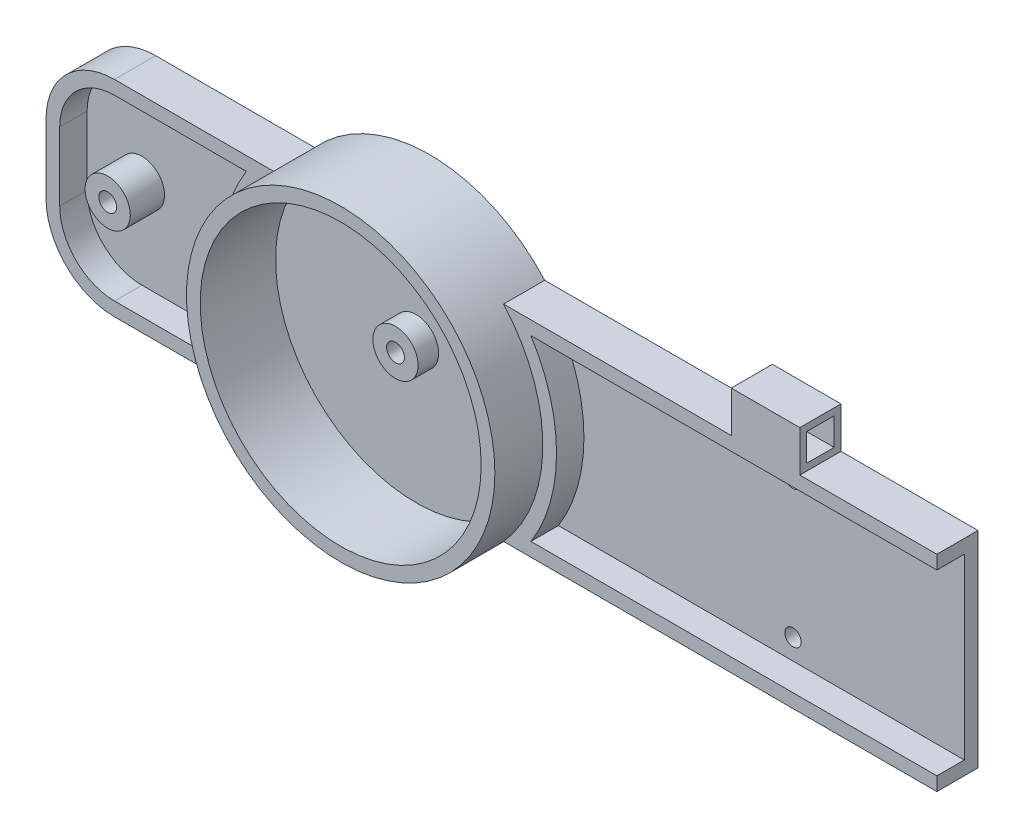
SolidWorks part; units mm, degrees
material "PLA"
ref_plane "Blat stołu" through (0, 0, 0) normal (0, 0, 1) x (1, 0, 0)
ref_plane "Płaszczyzna górna" through (0, 0, 0) normal (0, 1, 0) x (1, 0, 0)
ref_plane "Płaszczyzna prawa" through (0, 0, 0) normal (1, 0, 0) x (0, 0, -1)
sketch "Szkic1" plane through (0, 0, 0) normal (0, 0, 1) x (1, 0, 0)
  circle A3 centre (0, 0) radius 22.5
  dimension "D1" = 45
  dimension "D2" = 200
  dimension "D3" = 50
  dimension "D4" = 20
extrude "Dodanie-wyciągnięcie2" add sketch "Szkic1" along normal blind 13
sketch "Szkic2" plane through (0, 0, 0) normal (0, 0, 1) x (1, 0, 0)
  line L1 (-50, 15) -> (170, 15)
  line L2 (-50, 15) -> (-50, -15)
  line L3 (-50, -15) -> (170, -15)
  line L4 (170, 15) -> (170, -15)
  line L5 (-50, 15) -> (170, -15) construction
  line L6 (-50, -15) -> (170, 15) construction
  point P0 (60, 0)
  dimension "D1" = 30
  dimension "D2" = 50
  dimension "D3" = 220
extrude "Dodanie-wyciągnięcie3" add sketch "Szkic2" along normal blind 6
fillet "Zaokrąglenie1" radius 10 4 edges at (-50, -15, 3) (-50, 15, 3) (170, -15, 3) (170, 15, 3)
sketch "Szkic4" plane through (0, 0, 13) normal (0, 0, 1) x (1, 0, 0)
  circle A2 centre (0, 0) radius 20.5
  circle A3 centre (0, 0) radius 20.5
  dimension "D1" = 2
extrude "Wytnij-wyciągnięcie3" cut sketch "Szkic4" against normal blind 11
sketch "Szkic3" plane through (0, 0, 6) normal (0, 0, 1) x (1, 0, 0)
  line L3 (168, -5) -> (168, 5)
  line L4 (168, -5) -> (168, 5)
  line L5 (-48, 5) -> (-48, -5)
  line L6 (20.7666, -13) -> (160, -13)
  line L7 (-48, 5) -> (-48, -5)
  line L8 (160, 13) -> (20.7666, 13)
  line L9 (20.7666, -13) -> (160, -13)
  line L11 (160, 13) -> (20.7666, 13)
  line L14 (-20.7666, 13) -> (-40, 13)
  line L16 (-40, -13) -> (-20.7666, -13)
  line L17 (-20.7666, 13) -> (-40, 13)
  line L19 (-40, -13) -> (-20.7666, -13)
  arc A2 (20.7666, -13) -> (20.7666, 13) centre (0, 0) ccw
  arc A3 (20.7666, -13) -> (20.7666, 13) centre (0, 0) ccw
  arc A4 (-20.7666, 13) -> (-20.7666, -13) centre (0, 0) ccw
  arc A5 (-20.7666, 13) -> (-20.7666, -13) centre (0, 0) ccw
  arc A8 (160, -13) -> (168, -5) centre (160, -5) ccw
  arc A9 (160, -13) -> (168, -5) centre (160, -5) ccw
  arc A10 (168, 5) -> (160, 13) centre (160, 5) ccw
  arc A11 (168, 5) -> (160, 13) centre (160, 5) ccw
  arc A12 (-40, 13) -> (-48, 5) centre (-40, 5) ccw
  arc A13 (-40, 13) -> (-48, 5) centre (-40, 5) ccw
  arc A14 (-48, -5) -> (-40, -13) centre (-40, -5) ccw
  arc A15 (-48, -5) -> (-40, -13) centre (-40, -5) ccw
  dimension "D1" = 2
  dimension "D2" = 2
extrude "Wytnij-wyciągnięcie2" cut sketch "Szkic3" against normal blind 4
sketch "Szkic8" plane through (0, 0, 0) normal (0, 0, 1) x (1, 0, 0)
  line L1 (138.5, 7) -> (161.5, 7)
  line L2 (138.5, 7) -> (138.5, -7)
  line L3 (138.5, -7) -> (161.5, -7)
  line L4 (161.5, 7) -> (161.5, -7)
  line L5 (138.5, 7) -> (161.5, -7) construction
  line L6 (138.5, -7) -> (161.5, 7) construction
  point P0 (150, 0)
  dimension "D1" = 14
  dimension "D2" = 23
  dimension "D3" = 150
extrude "Wytnij-wyciągnięcie4" cut sketch "Szkic8" along normal up to next
sketch "Szkic12" plane through (0, 0, 2) normal (0, 0, 1) x (1, 0, 0)
  circle A0 centre (0, 0) radius 3.3
  dimension "D1" = 6.6
extrude "Dodanie-wyciągnięcie4" add sketch "Szkic12" along normal blind 3
hole_wizard "Otwór pod śrubę M21" positions "Szkic5" profile "Szkic6" hole size "M2" standard "ISO" end condition up to next
sketch "Szkic5" plane through (0, 0, 0) normal (0, 0, 1) x (1, 0, 0)
  point P0 (0, 0)
sketch "Szkic6" plane through (0, 0, 0) normal (1, 0, 0) x (0, 1, 0)
  line L0 (0, 0) -> (0, 5)
  line L1 (0, 5) -> (1.3, 5)
  line L2 (1.3, 5) -> (1.3, 0)
  line L5 (1.3, 0) -> (0, 0)
  line L11 (0, -6.35) -> (0, 107.95) construction
  dimension "Średnica otworu na wylot" = 2.6
  dimension "Głębokość otworu na wylot" = 5
hole_wizard "Otwór pod śrubę M23" positions "Szkic9" profile "Szkic10" hole size "M2" standard "ISO" end condition up to next
sketch "Szkic9" plane through (0, 0, 0) normal (0, 0, 1) x (1, 0, 0)
  line L0 (138.5, 7) -> (138.5, -7) construction
  point P0 (136, 0)
  point P2 (164, 0)
  dimension "D1" = 2.5
  dimension "D2" = 3
  dimension "D3" = 28
sketch "Szkic10" plane through (136, 0, 0) normal (1, 0, 0) x (0, 1, 0)
  line L0 (0, 0) -> (0, 2)
  line L1 (0, 2) -> (1.3, 2)
  line L2 (1.3, 2) -> (1.3, 0)
  line L5 (1.3, 0) -> (0, 0)
  line L11 (0, -6.35) -> (0, 107.95) construction
  dimension "Średnica otworu na wylot" = 2.6
  dimension "Głębokość otworu na wylot" = 2
sketch "Szkic14" plane through (0, 0, 2) normal (0, 0, 1) x (1, 0, 0)
  circle A0 centre (-40, 0) radius 3.3
  dimension "D1" = 40
  dimension "D2" = 40
extrude "Dodanie-wyciągnięcie5" add sketch "Szkic14" along normal blind 5
hole_wizard "Otwór pod śrubę M24" positions "Szkic 3D2" profile "Szkic11" hole size "M2" standard "ISO" end condition through all
sketch3d "Szkic 3D2"
  point P0 (-40, 0, 0)
  dimension "D1" = 40
sketch "Szkic11" plane through (-40, 0, 0) normal (1, 0, 0) x (0, 1, 0)
  line L0 (0, 0) -> (0, 13)
  line L1 (0, 13) -> (1.3, 13)
  line L2 (1.3, 13) -> (1.3, 0)
  line L5 (1.3, 0) -> (0, 0)
  line L11 (0, -6.35) -> (0, 107.95) construction
  dimension "Średnica otworu na wylot" = 2.6
  dimension "Głębokość otworu na wylot" = 13
ref_plane "Płaszczyzna1" through (130, 0, 0) normal (1, 0, 0) x (0, 0, -1)
sketch "Szkic15" plane through (130, 0, 0) normal (1, 0, 0) x (0, 0, -1)
  line L0 (-6, 15) -> (0, 15) construction
  line L1 (-6, 15) -> (0, 15)
  line L2 (-6, 15) -> (-6, 21)
  line L3 (-6, 21) -> (0, 21)
  line L4 (0, 15) -> (0, 21)
  line L5 (-6, 15) -> (0, 21) construction
  line L6 (-6, 21) -> (0, 15) construction
  line L7 (0, 5) -> (0, 15) construction
  line L8 (-6, 15) -> (-6, 5) construction
  line L9 (-5, 20) -> (-1, 20)
  line L10 (-1, 16) -> (-1, 20)
  line L11 (-5, 16) -> (-1, 16)
  line L12 (-5, 16) -> (-5, 20)
  point P0 (-3, 18)
  dimension "D1" = 6
  dimension "D2" = 1
extrude "Dodanie-wyciągnięcie6" add sketch "Szkic15" against normal blind 10
pattern_linear "Szyk liniowy1" count 2 spacing 70 along (-1, 0, 0) of "Dodanie-wyciągnięcie6"
sketch "Szkic17" plane through (0, 0, 2) normal (0, 0, 1) x (1, 0, 0)
  line L0 (50, 15) -> (16.7705, 15) construction
  line L1 (105, -10) -> (55, -10)
  line L2 (105, -10) -> (105, 10)
  line L3 (105, 10) -> (55, 10)
  line L4 (55, -10) -> (55, 10)
  line L5 (105, -10) -> (55, 10) construction
  line L6 (105, 10) -> (55, -10) construction
  point P0 (80, 0)
  dimension "D1" = 50
  dimension "D2" = 20
  dimension "D3" = 80
  dimension "D4" = 15
hole_wizard "Otwór pod śrubę M25" positions "Szkic18" profile "Szkic19" hole size "M2" standard "ISO" end condition through all
sketch "Szkic18" plane through (0, 0, 2) normal (0, 0, 1) x (1, 0, 0)
  point P0 (55, -10)
  point P3 (105, -10)
  point P6 (105, 10)
  point P9 (55, 10)
sketch "Szkic19" plane through (55, -10, 2) normal (1, 0, 0) x (0, -1, 0)
  line L0 (0, 0) -> (0, 2)
  line L1 (0, 2) -> (1.2, 2)
  line L2 (1.2, 2) -> (1.2, 0)
  line L5 (1.2, 0) -> (0, 0)
  line L11 (0, -6.35) -> (0, 107.95) construction
  dimension " rednica otworu na wylot" = 2.4
  dimension "G³êboko æ otworu na wylot" = 2
ref_plane "Płaszczyzna2" through (80, 0, 0) normal (1, 0, 0) x (0, 0, -1)
other "Cięcie powierzchnią1"
